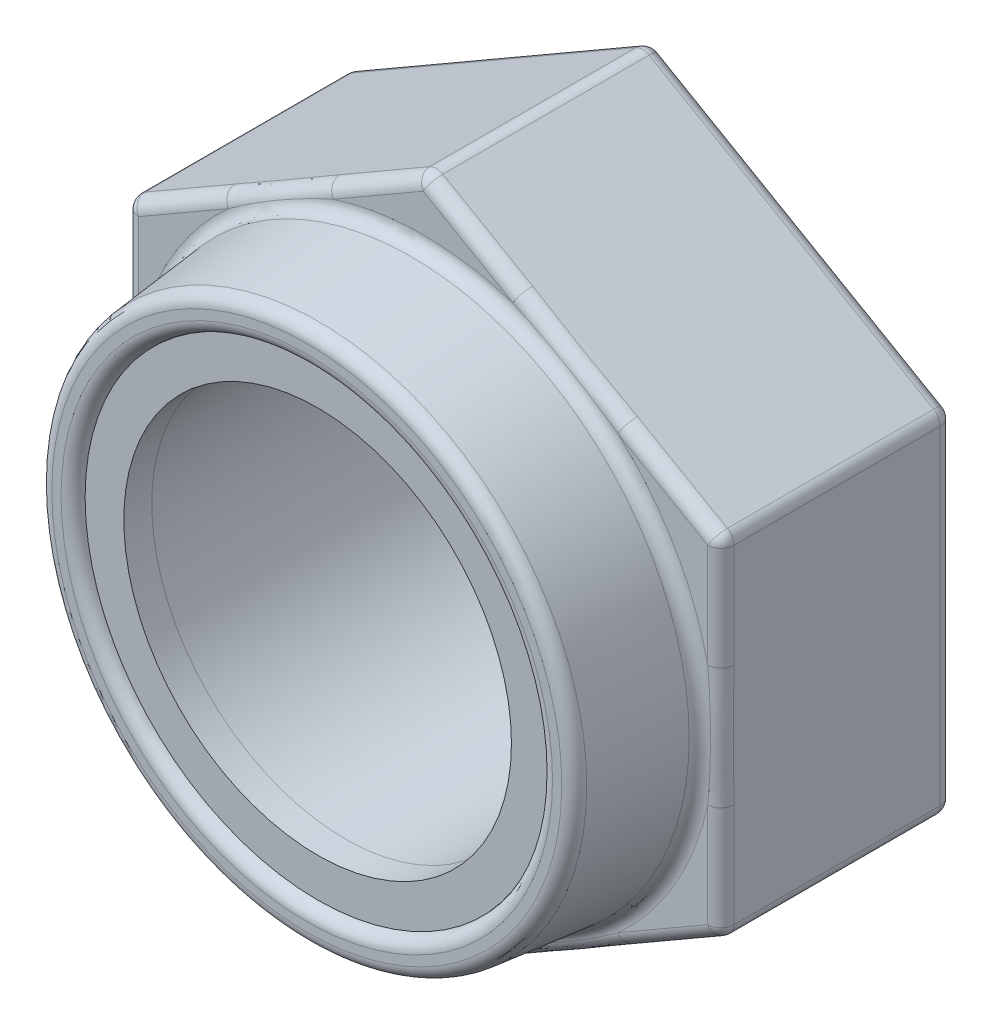
SolidWorks part; units mm, degrees
ref_plane "Front Plane" through (0, 0, 0) normal (0, 0, 1) x (1, 0, 0)
ref_plane "Top Plane" through (0, 0, 0) normal (0, 1, 0) x (1, 0, 0)
ref_plane "Right Plane" through (0, 0, 0) normal (1, 0, 0) x (0, 0, -1)
sketch "Sketch1" plane through (0, 0, 0) normal (0, 0, 1) x (1, 0, 0)
  line L1 (3.8408, -2.2175) -> (3.8408, 2.2175)
  line L2 (3.8408, 2.2175) -> (0, 4.435)
  line L3 (0, 4.435) -> (-3.8408, 2.2175)
  line L4 (-3.8408, 2.2175) -> (-3.8408, -2.2175)
  line L5 (-3.8408, -2.2175) -> (0, -4.435)
  line L6 (0, -4.435) -> (3.8408, -2.2175)
  circle A0 centre (0, 0) radius 3.8408 construction
  dimension "D1" = 8.87
extrude "Boss-Extrude1" add sketch "Sketch1" along normal blind 3
sketch "Sketch2" plane through (0, 0, 3) normal (0, 0, 1) x (1, 0, 0)
  circle A0 centre (0, 0) radius 3.6
  dimension "D1" = 7.2
extrude "Boss-Extrude2" add sketch "Sketch2" along normal blind 1.5 draft 6
sketch "Sketch3" plane through (0, 0, 4.5) normal (0, 0, 1) x (1, 0, 0)
  circle A0 centre (0, 0) radius 2.5
  dimension "D1" = 5
extrude "Cut-Extrude1" cut sketch "Sketch3" against normal through all contours A0
sketch "Sketch4" plane through (0, 0, 4.5) normal (0, 0, 1) x (1, 0, 0)
  circle A2 centre (0, 0) radius 3
  circle A3 centre (0, 0) radius 3
  dimension "D1" = 0.5
extrude "Cut-Extrude2" cut sketch "Sketch4" against normal blind 0.5
fillet "Fillet2" radius 0.17 1 edges at (3.4423, 0, 4.5)
fillet "Fillet3" radius 0.17 1 edges at (3, 0, 4.5)
sketch "Sketch5" plane through (0, 0, 4) normal (0, 0, 1) x (1, 0, 0)
  circle A1 centre (0, 0) radius 3
  circle A2 centre (0, 0) radius 3
  dimension "D1" = 0
ref_plane "Plane1" through (0, 0, 6.53) normal (0, 0, 1) x (1, 0, 0)
sketch "Sketch6" plane through (0, 0, 6.53) normal (0, 0, 1) x (1, 0, 0)
  circle A1 centre (0, 0) radius 3 construction
  circle A2 centre (0, 0) radius 3
extrude "Boss-Extrude4" add sketch "Sketch5" along normal blind 0.36 separate body contours A2
sketch "Sketch8" plane through (0, 0, 4.36) normal (0, 0, 1) x (1, 0, 0)
  circle A0 centre (0, 0) radius 2.5 construction
  circle A3 centre (0, 0) radius 2.5
extrude "Cut-Extrude3" cut sketch "Sketch8" against normal blind 0.36 contours A3
fillet "Fillet4" radius 0.17 1 edges at (3.6, 0, 3)
fillet "Fillet5" radius 0.17 18 edges at (-1.9204, 3.3263, 3) (-1.9204, 3.3263, 0) (-3.8408, 2.2175, 1.5) (-3.8408, 0, 3) (-3.8408, 0, 0) (-3.8408, -2.2175, 1.5) (-1.9204, -3.3262, 3) (-1.9204, -3.3262, 0) (0, -4.435, 1.5) (1.9204, -3.3263, 3) (1.9204, -3.3263, 0) (3.8408, -2.2175, 1.5) (3.8408, 0, 3) (3.8408, 0, 0) (3.8408, 2.2175, 1.5) (1.9204, 3.3263, 3) (0, 4.435, 1.5) (1.9204, 3.3263, 0)
